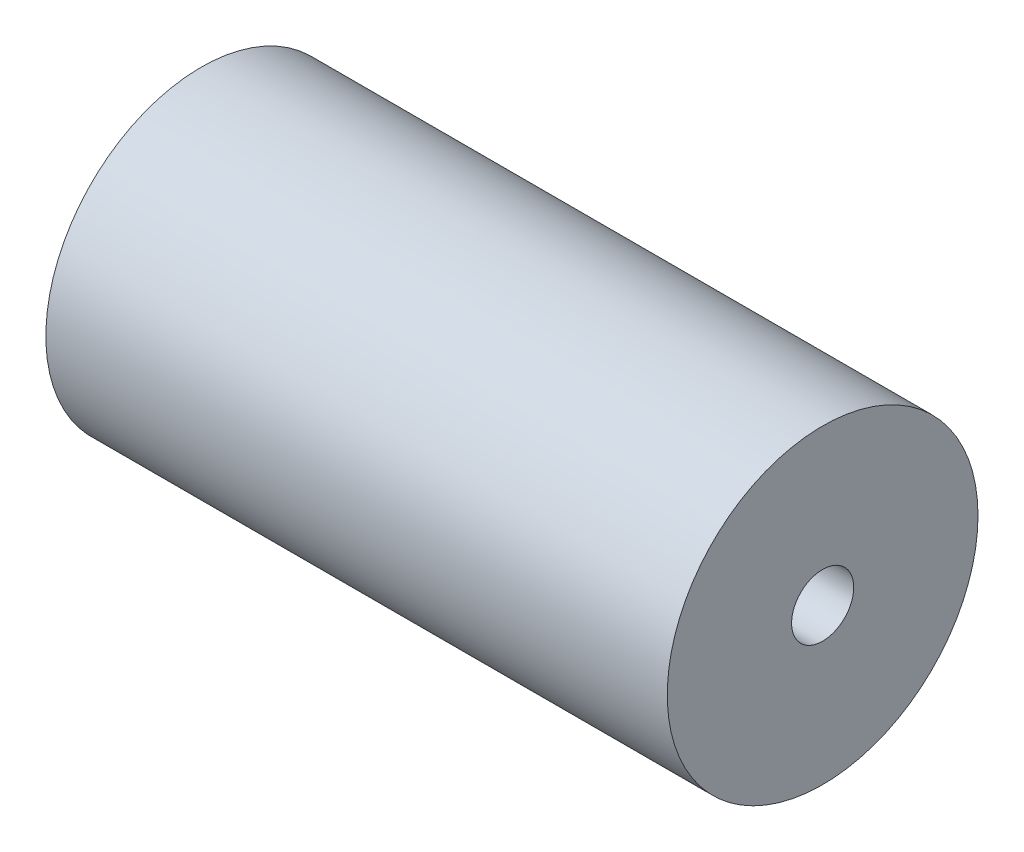
SolidWorks part; units mm, degrees
ref_plane "Front" through (0, 0, 0) normal (0, 0, 1) x (1, 0, 0)
ref_plane "Top" through (0, 0, 0) normal (0, 1, 0) x (1, 0, 0)
ref_plane "Right" through (0, 0, 0) normal (1, 0, 0) x (0, 0, -1)
sketch "Sketch1" plane through (0, 0, 0) normal (1, 0, 0) x (0, 0, -1)
  circle A0 centre (0, 0) radius 0.5
  circle A1 centre (0, 0) radius 2.5
  dimension "D1" = 1
  dimension "D2" = 5
extrude "Boss-Extrude1" add sketch "Sketch1" along normal blind 10
